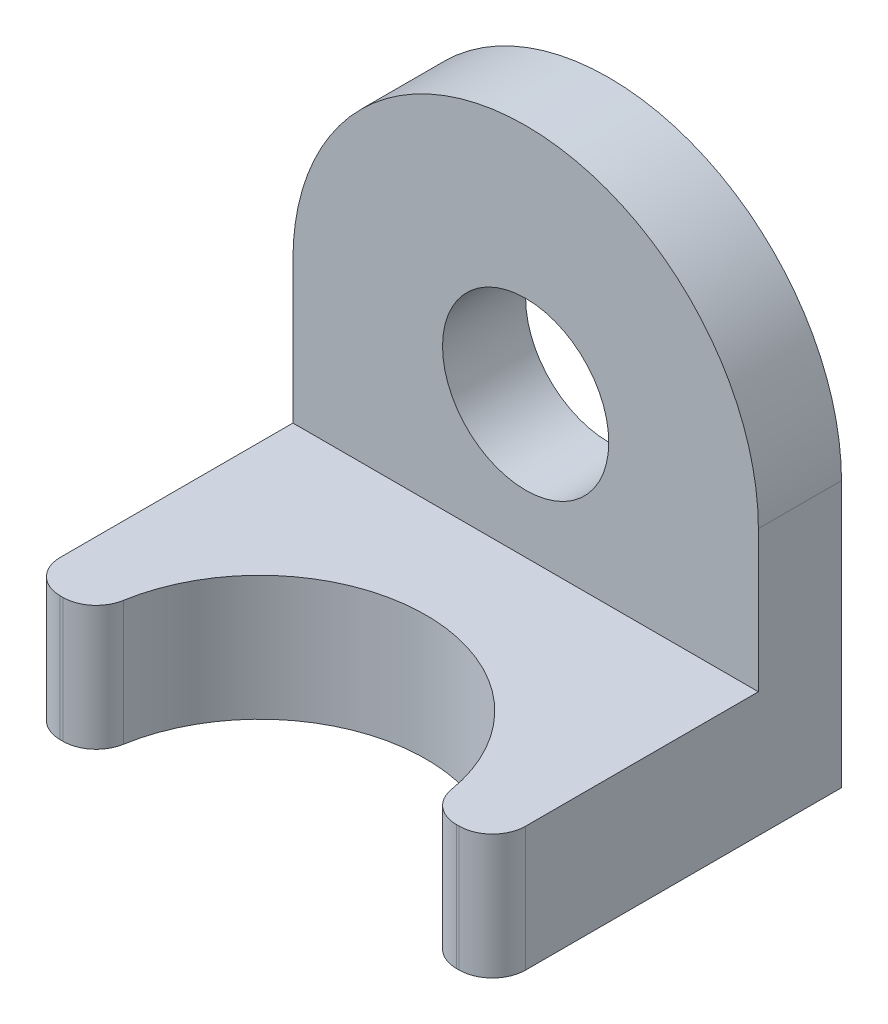
SolidWorks part; units mm, degrees
ref_plane "Front Plane" through (0, 0, 0) normal (0, 0, 1) x (1, 0, 0)
ref_plane "Top Plane" through (0, 0, 0) normal (0, 1, 0) x (1, 0, 0)
ref_plane "Right Plane" through (0, 0, 0) normal (1, 0, 0) x (0, 0, -1)
sketch "Sketch1" plane through (0, 0, 0) normal (0, 0, 1) x (1, 0, 0)
  line L0 (-8.89, 0) -> (-8.89, -10.16)
  line L1 (-8.89, -10.16) -> (8.89, -10.16)
  line L2 (8.89, -10.16) -> (8.89, 0)
  circle A0 centre (0, 0) radius 3.175
  arc A1 (8.89, 0) -> (-8.89, 0) centre (0, 0) ccw
  dimension "D1" = 6.35
  dimension "D2" = 17.78
  dimension "D3" = 10.16
extrude "Boss-Extrude1" add sketch "Sketch1" along normal blind 3.175
sketch "Sketch2" plane through (0, 0, 3.175) normal (0, 0, 1) x (1, 0, 0)
  line L0 (8.89, -10.16) -> (8.89, 0) construction
  line L1 (-8.89, -10.16) -> (8.89, -10.16)
  line L2 (-8.89, -10.16) -> (-8.89, -5.3975)
  line L3 (-8.89, -5.3975) -> (8.89, -5.3975)
  line L4 (8.89, -10.16) -> (8.89, -5.3975)
  dimension "D1" = 4.7625
extrude "Boss-Extrude2" add sketch "Sketch2" along normal blind 10.16
sketch "Sketch3" plane through (0, -10.16, 0) normal (0, -1, 0) x (-1, 0, 0)
  line L0 (8.89, -13.335) -> (-8.89, -13.335) construction
  circle A0 centre (0, -13.335) radius 6.35
  dimension "D1" = 12.7
extrude "Cut-Extrude1" cut sketch "Sketch3" against normal blind 17.78
fillet "Fillet2" radius 1.27 2 edges at (-8.89, -7.7788, 13.335) (8.89, -7.7788, 13.335)
fillet "Fillet3" radius 1.27 2 edges at (-6.35, -7.7788, 13.335) (6.35, -7.7788, 13.335)
